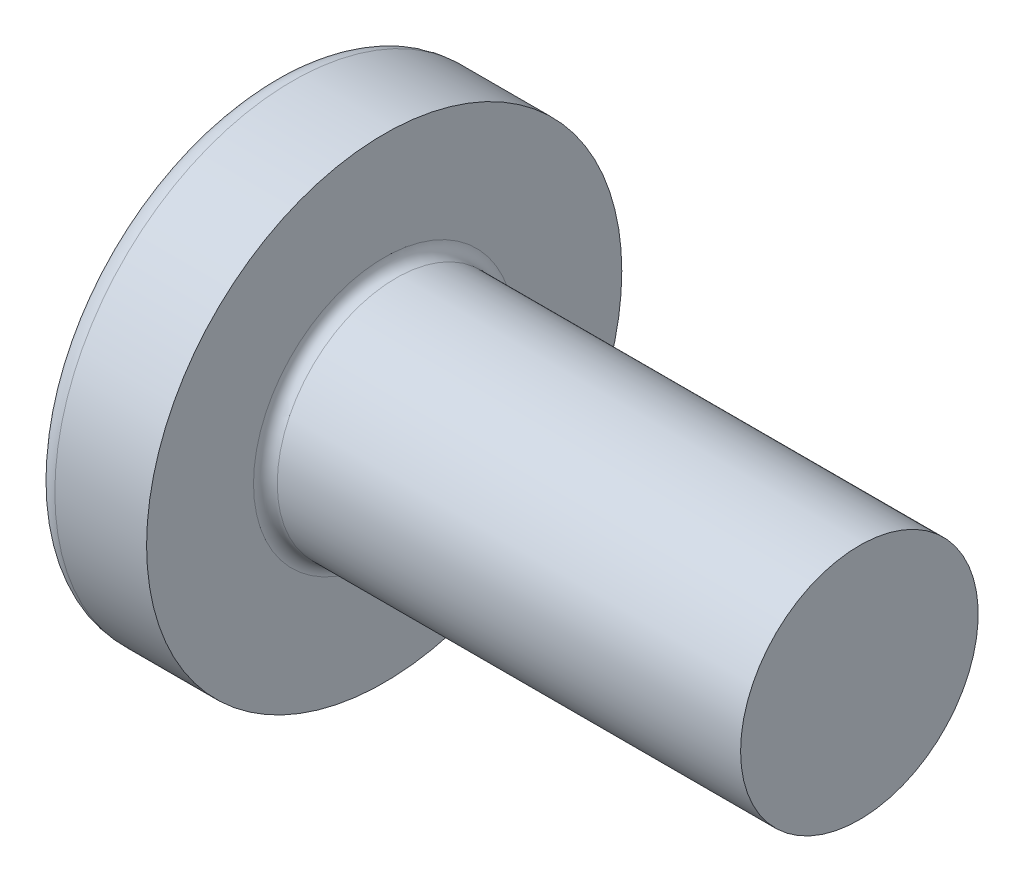
SolidWorks part; units mm, degrees
ref_plane "Plane1" through (0, 0, 0) normal (0, 0, 1) x (1, 0, 0)
ref_plane "Plane2" through (0, 0, 0) normal (0, 1, 0) x (1, 0, 0)
ref_plane "Plane3" through (0, 0, 0) normal (1, 0, 0) x (0, 0, -1)
sketch "BodySke" plane through (0, 0, 0) normal (0, 0, 1) x (1, 0, 0)
  line L0 (3.1, 2) -> (3.1, 4)
  line L1 (3.45, 6.35) -> (3.45, -3.175) construction
  line L2 (-25.4, 0) -> (127, 0) construction
  line L3 (11.1, 0) -> (0, 0)
  line L4 (3.1, 2) -> (11.1, 2)
  line L5 (11.1, 2) -> (11.1, 0)
  line L6 (1.5553, 4) -> (3.1, 4)
  line L8 (3.1, 6.35) -> (3.1, -3.175) construction
  arc A0 (1.2654, 3.8534) -> (0, 0) centre (6.5, 0) ccw
  arc A2 (1.2654, 3.8534) -> (1.5553, 4) centre (1.5553, 3.64) cw
  dimension "Head_fillet_rad" = 0.36
  dimension "Head_crown_rad" = 6.5
  dimension "Head_ht" = 3.1
  dimension "Diameter" = 4
  dimension "Length" = 8
  dimension "Head_dia" = 8
  dimension "Advance" = 0.7
  dimension "Thread_nom" = 8
revolve "Base-Revolve" add sketch "BodySke"
cosmetic thread "ThreadCosmetic"
fillet "Fillet1" radius 0.2
sketch "Sketch3" plane through (0, 0, 0) normal (1, 0, 0) x (0, 0, -1)
  line L0 (0.515, -2.15) -> (-0.515, -2.15)
  line L1 (0.515, -2.15) -> (0.515, 2.15)
  line L2 (-0.515, 2.15) -> (0.515, 2.15)
  line L3 (-0.515, 2.15) -> (-0.515, -2.15)
  dimension "D1" = 2.15
  dimension "Cross_dia" = 4.3
  dimension "D2" = 0.515
  dimension "Cross_width" = 1.03
ref_plane "Plane4" through (2.34, 0, 0) normal (1, 0, 0) x (0, 0, -1)
sketch "Sketch4" plane through (2.34, 0, 0) normal (1, 0, 0) x (0, 0, -1)
  line L0 (0.515, -0.9833) -> (-0.515, -0.9833)
  line L1 (0.515, -0.9833) -> (0.515, 0.9833)
  line L2 (-0.515, 0.9833) -> (0.515, 0.9833)
  line L3 (-0.515, 0.9833) -> (-0.515, -0.9833)
  dimension "D1" = 1.03
  dimension "D2" = 1.9666
  dimension "D3" = 0.515
  dimension "D4" = 0.9833
loft "Recess" cut profiles "Sketch3", "Sketch4"
pattern_circular "RecPat" count 2 every 90
sketch "RecCorSke" plane through (0, 0, 0) normal (0, 0, 1) x (1, 0, 0)
  line L0 (-3.175, 0) -> (15.875, 0) construction
  line L1 (-25.4, 0) -> (127, 0) construction
  line L2 (0, 0) -> (0, 1.0146)
  line L3 (0, 1.0146) -> (2.34, 0.851)
  line L4 (2.34, 0.851) -> (2.6165, 0)
  line L5 (2.6165, 0) -> (0, 0)
  dimension "Diameter" = 1.702
  dimension "Depth" = 2.34
  dimension "Draft_angle" = 4
  dimension "Bottom_angle" = 18
revolve "RecessCore" cut sketch "RecCorSke" angle 360 about L0
sketch "ThdSchSke" plane through (0, 0, 0) normal (0, 0, 1) x (1, 0, 0)
  line L0 (4.5, -1.61) -> (4.2269, -2)
  line L1 (4.5, -1.61) -> (4.7731, -2)
  line L2 (4.7731, -2) -> (4.7731, -2.5)
  line L3 (-3.175, 0) -> (5.1513, 0) construction
  line L5 (4.7731, -2.5) -> (4.2269, -2.5)
  line L6 (4.2269, -2.5) -> (4.2269, -2)
  dimension "Thread_minor" = 3.22
  dimension "Diameter" = 4
  dimension "Start" = 4.5
  dimension "SideAngle" = 55
  dimension "VeeAngle" = 70
  dimension "Overcut" = 5
revolve "ThreadSchematic" [suppressed] cut sketch "ThdSchSke" angle 360 about L3
pattern_linear "ThdSchPat" [suppressed]
equation "\"D1@Sketch3\" = \"Cross_dia@Sketch3\" / 2"
equation "\"D2@Sketch3\" = \"Cross_width@Sketch3\" / 2"
equation "\"Depth@RecCorSke\" = \"Cross_depth@Plane4\""
equation "\"D1@Sketch4\" = \"Cross_width@Sketch3\""
equation "\"D2@Sketch4\" = \"Cross_dia@Sketch3\" - 2.0 * \"Cross_depth@Plane4\" * tan(26.5  * 0.017453292)"
equation "\"D3@Sketch4\" = \"D1@Sketch4\" / 2"
equation "\"D4@Sketch4\" = \"D2@Sketch4\" / 2"
equation "\"Thread_length@ThreadCosmetic\" = ((sgn( (\"Length@BodySke\" - \"Advance@BodySke\" * 2.0 ) - \"Thread_nom@BodySke\" )-1)*( (\"Length@BodySke\" - \"Advance@BodySke\" * 2.0 ) - \"Thread_nom@BodySke\" ))/-2+ \"Thread_nom@BodySke\""
equation "\"Thread_minor@ThdSchSke\" = \"Thread_minor@ThreadCosmetic\""
equation "\"Diameter@ThdSchSke\" = \"Diameter@BodySke\""
equation "\"Overcut@ThdSchSke\" = \"Diameter@BodySke\" * 1.25"
equation "\"Start@ThdSchSke\" = \"Head_ht@BodySke\" + \"Length@BodySke\" - \"Thread_length@ThreadCosmetic\"  '---Non-countersunk---"
equation "\"Num_threads@ThdSchPat\" = int( \"Thread_length@ThreadCosmetic\" / \"Advance@BodySke\" + 0.999 )  + 1"
equation "\"Advance@ThdSchPat\" = \"Thread_length@ThreadCosmetic\" /  (\"Num_threads@ThdSchPat\" - 1) 'relax it"
